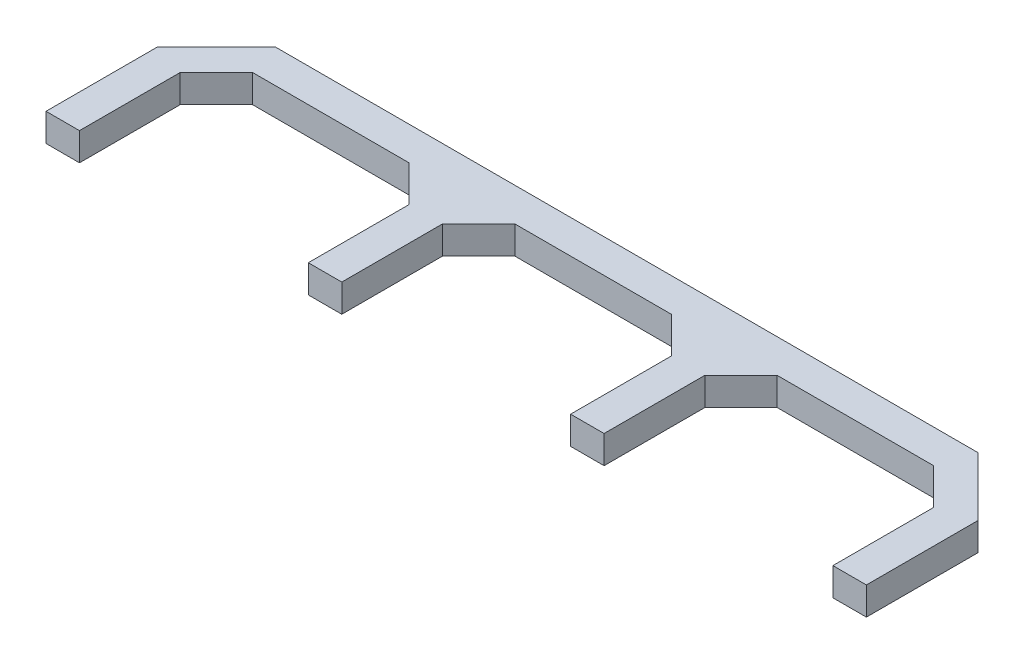
SolidWorks part; units mm, degrees
ref_plane "Front Plane" through (0, 0, 0) normal (0, 0, 1) x (1, 0, 0)
ref_plane "Top Plane" through (0, 0, 0) normal (0, 1, 0) x (1, 0, 0)
ref_plane "Right Plane" through (0, 0, 0) normal (1, 0, 0) x (0, 0, -1)
sketch "Sketch1" plane through (0, 0, 0) normal (0, 1, 0) x (1, 0, 0)
  line L0 (-38.7942, 34.7998) -> (-49.3236, 24.2704)
  line L1 (-49.3236, 4.2704) -> (-43.3236, 4.2704)
  line L2 (-49.3236, 4.2704) -> (-49.3236, 24.2704)
  line L3 (-2.3236, 22.3098) -> (-8.8136, 28.7998)
  line L4 (-2.3236, 4.2704) -> (3.6764, 4.2704)
  line L5 (87.1469, 34.7998) -> (-38.7942, 34.7998)
  line L6 (-43.3236, 4.2704) -> (-43.3236, 22.3098)
  line L7 (-43.3236, 22.3098) -> (-36.8336, 28.7998)
  line L8 (-36.8336, 28.7998) -> (-8.8136, 28.7998)
  line L9 (24.1764, 34.7998) -> (24.1764, 28.7998) construction
  line L10 (44.6764, 22.3098) -> (38.1864, 28.7998)
  line L11 (44.6764, 22.3098) -> (44.6764, 4.2704)
  line L12 (50.6764, 22.3098) -> (50.6764, 4.2704)
  line L13 (-2.3236, 22.3098) -> (-2.3236, 4.2704)
  line L14 (85.1864, 28.7998) -> (57.1664, 28.7998)
  line L15 (91.6764, 22.3098) -> (85.1864, 28.7998)
  line L16 (3.6764, 22.3098) -> (3.6764, 4.2704)
  line L17 (10.1664, 28.7998) -> (38.1864, 28.7998)
  line L18 (91.6764, 4.2704) -> (91.6764, 22.3098)
  line L19 (50.6764, 4.2704) -> (44.6764, 4.2704)
  line L20 (50.6764, 22.3098) -> (57.1664, 28.7998)
  line L21 (97.6764, 4.2704) -> (97.6764, 24.2704)
  line L22 (97.6764, 4.2704) -> (91.6764, 4.2704)
  line L23 (87.1469, 34.7998) -> (97.6764, 24.2704)
  line L29 (3.6764, 22.3098) -> (10.1664, 28.7998)
  dimension "D1" = 135
  dimension "D2" = 20
  dimension "D3" = 41
  dimension "D4" = 6
  dimension "D5" = 62.9706
  dimension "D6" = 9.1782
  dimension "D7" = 225
  dimension "D8" = 28.02
  dimension "D9" = 14.8909
  dimension "D10" = 135
  dimension "D11" = 225
  dimension "D12" = 18.0394
  dimension "D13" = 18.0394
  dimension "D14" = 18.0394
  dimension "D16" = 6
  dimension "D21" = 9.1782
extrude "Boss-Extrude1" add sketch "Sketch1" along normal blind 5
